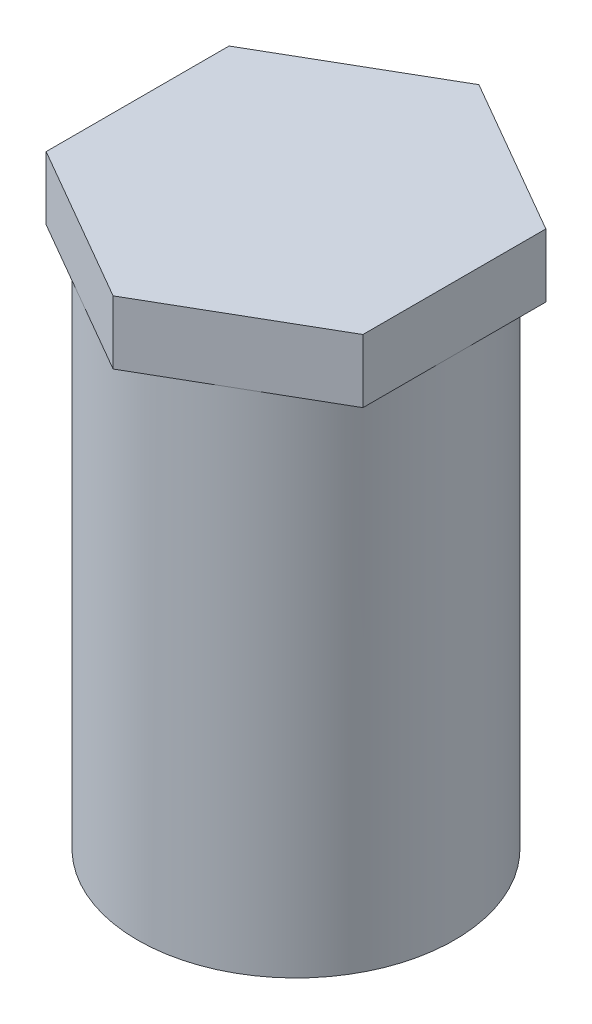
SolidWorks part; units mm, degrees
ref_plane "Front Plane" through (0, 0, 0) normal (0, 0, 1) x (1, 0, 0)
ref_plane "Top Plane" through (0, 0, 0) normal (0, 1, 0) x (1, 0, 0)
ref_plane "Right Plane" through (0, 0, 0) normal (1, 0, 0) x (0, 0, -1)
sketch "Sketch1" plane through (0, 0, 0) normal (0, 1, 0) x (1, 0, 0)
  circle A0 centre (0, 0) radius 12.5
  dimension "D1" = 25
extrude "Boss-Extrude1" add sketch "Sketch1" along normal blind 40
sketch "Sketch2" plane through (0, 40, 0) normal (0, 1, 0) x (1, 0, 0)
  line L1 (0, -14.4338) -> (12.5, -7.2169)
  line L2 (12.5, -7.2169) -> (12.5, 7.2169)
  line L3 (12.5, 7.2169) -> (0, 14.4338)
  line L4 (0, 14.4338) -> (-12.5, 7.2169)
  line L5 (-12.5, 7.2169) -> (-12.5, -7.2169)
  line L6 (-12.5, -7.2169) -> (0, -14.4338)
  circle A0 centre (0, 0) radius 12.5 construction
  dimension "D1" = 25
extrude "Boss-Extrude2" add sketch "Sketch2" along normal blind 5
